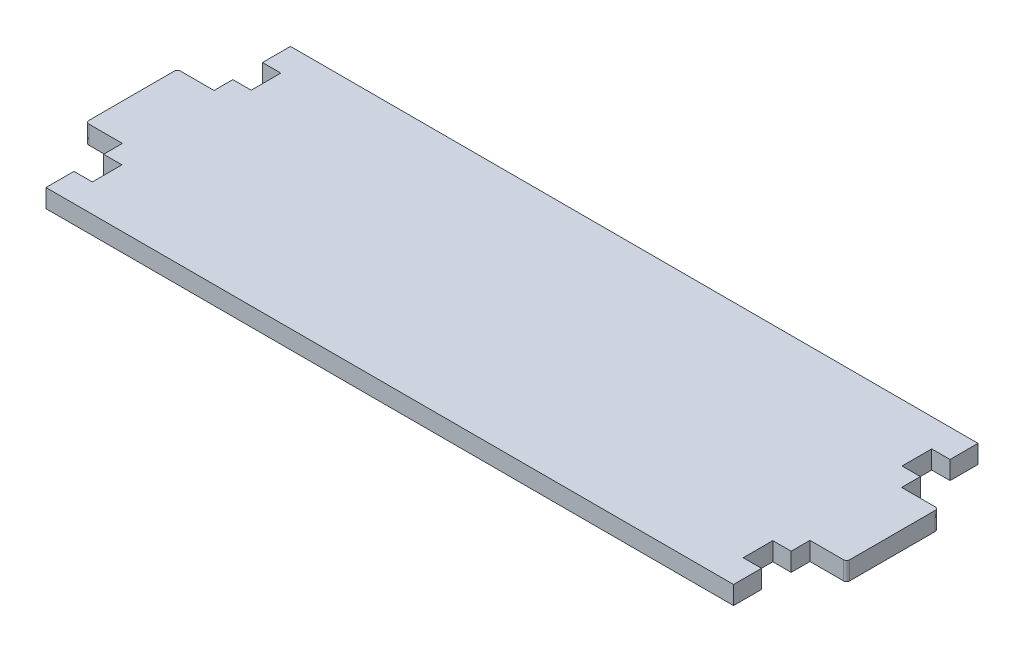
SolidWorks part; units mm, degrees
ref_plane "Спереди" through (0, 0, 0) normal (0, 0, 1) x (1, 0, 0)
ref_plane "Сверху" through (0, 0, 0) normal (0, 1, 0) x (1, 0, 0)
ref_plane "Справа" through (0, 0, 0) normal (1, 0, 0) x (0, 0, -1)
sketch "Эскиз1" plane through (0, 0, 0) normal (0, 1, 0) x (1, 0, 0)
  line L0 (0, 0) -> (0, 15.581) construction
  line L1 (-56.25, 20) -> (56.25, 20)
  line L2 (-56.25, 20) -> (-56.25, -20)
  line L3 (-56.25, -20) -> (56.25, -20)
  line L4 (56.25, 20) -> (56.25, -20)
  line L5 (-56.25, 20) -> (56.25, -20) construction
  line L6 (-56.25, -20) -> (56.25, 20) construction
  line L7 (56.25, 7.5) -> (62.25, 7.5)
  line L8 (56.25, 7.5) -> (56.25, -7.5)
  line L9 (56.25, -7.5) -> (62.25, -7.5)
  line L10 (62.25, 7.5) -> (62.25, -7.5)
  line L11 (56.25, 7.5) -> (62.25, -7.5) construction
  line L12 (56.25, -7.5) -> (62.25, 7.5) construction
  line L13 (-56.25, -7.5) -> (-62.25, 7.5) construction
  line L14 (-56.25, 7.5) -> (-62.25, -7.5) construction
  line L15 (-62.25, 7.5) -> (-62.25, -7.5)
  line L16 (-56.25, -7.5) -> (-62.25, -7.5)
  line L17 (-56.25, 7.5) -> (-56.25, -7.5)
  line L18 (-56.25, 7.5) -> (-62.25, 7.5)
  line L19 (0, 0) -> (11.3485, 0) construction
  line L20 (53.25, 15.425) -> (56.25, 15.425)
  line L21 (53.25, 15.425) -> (53.25, 10.575)
  line L22 (53.25, 10.575) -> (56.25, 10.575)
  line L23 (56.25, 15.425) -> (56.25, 10.575)
  line L24 (53.25, 15.425) -> (56.25, 10.575) construction
  line L25 (53.25, 10.575) -> (56.25, 15.425) construction
  line L26 (53.25, -10.575) -> (56.25, -15.425) construction
  line L27 (53.25, -15.425) -> (56.25, -10.575) construction
  line L28 (56.25, -15.425) -> (56.25, -10.575)
  line L29 (53.25, -10.575) -> (56.25, -10.575)
  line L30 (53.25, -15.425) -> (53.25, -10.575)
  line L31 (53.25, -15.425) -> (56.25, -15.425)
  line L32 (-53.25, 10.575) -> (-56.25, 15.425) construction
  line L33 (-53.25, 15.425) -> (-56.25, 10.575) construction
  line L34 (-56.25, 15.425) -> (-56.25, 10.575)
  line L35 (-53.25, 10.575) -> (-56.25, 10.575)
  line L36 (-53.25, 15.425) -> (-53.25, 10.575)
  line L37 (-53.25, 15.425) -> (-56.25, 15.425)
  line L38 (-53.25, -15.425) -> (-56.25, -10.575) construction
  line L39 (-53.25, -10.575) -> (-56.25, -15.425) construction
  line L40 (-53.25, -15.425) -> (-56.25, -15.425)
  line L41 (-53.25, -15.425) -> (-53.25, -10.575)
  line L42 (-53.25, -10.575) -> (-56.25, -10.575)
  line L43 (-56.25, -15.425) -> (-56.25, -10.575)
  point P0 (0, 0)
  point P6 (59.25, 0)
  point P17 (-59.25, 0)
  point P18 (54.75, 13)
  point P28 (54.75, -13)
  point P33 (-54.75, 13)
  point P38 (-54.75, -13)
  point P39 (53.1991, 10.575)
  dimension "D1" = 40
  dimension "D2" = 6
  dimension "D3" = 15
  dimension "D4" = 112.5
  dimension "D5" = 5.5
  dimension "D6" = 4.85
  dimension "D7" = 3
extrude "Бобышка-Вытянуть1" add sketch "Эскиз1" along normal blind 3 contours L4 L1 L2 L3 | L10 L7 L4 L9 | L2 L18 L15 L16
fillet "Скругление1" radius 0.5 4 edges at (-62.25, 1.5, -7.5) (-62.25, 1.5, 7.5) (62.25, 1.5, -7.5) (62.25, 1.5, 7.5)
